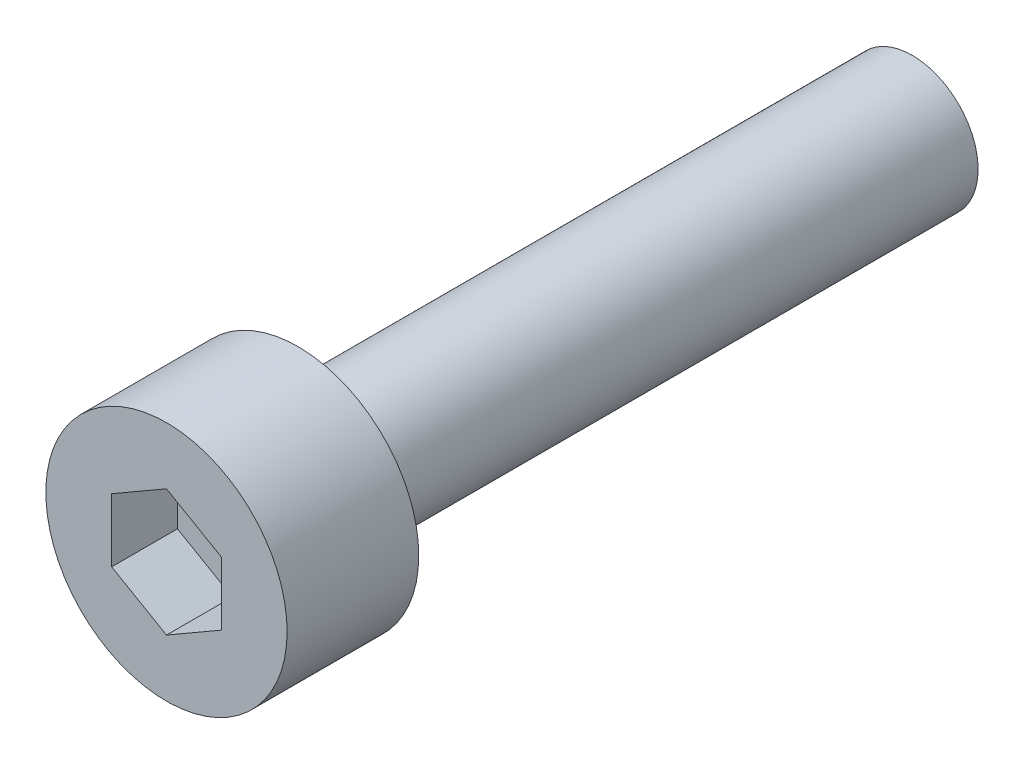
SolidWorks part; units mm, degrees
material "灰铸铁"
ref_plane "前视基准面" through (0, 0, 0) normal (0, 0, 1) x (1, 0, 0)
ref_plane "上视基准面" through (0, 0, 0) normal (0, 1, 0) x (1, 0, 0)
ref_plane "右视基准面" through (0, 0, 0) normal (1, 0, 0) x (0, 0, -1)
sketch "草图1" plane through (0, 0, 0) normal (0, 0, 1) x (1, 0, 0)
  circle A0 centre (0, 0) radius 2.75
  dimension "D1" = 5.5
extrude "凸台-拉伸1" add sketch "草图1" along normal blind 3
sketch "草图2" plane through (0, 0, 3) normal (0, 0, 1) x (1, 0, 0)
  line L1 (0, -1.4434) -> (1.25, -0.7217)
  line L2 (1.25, -0.7217) -> (1.25, 0.7217)
  line L3 (1.25, 0.7217) -> (0, 1.4434)
  line L4 (0, 1.4434) -> (-1.25, 0.7217)
  line L5 (-1.25, 0.7217) -> (-1.25, -0.7217)
  line L6 (-1.25, -0.7217) -> (0, -1.4434)
  circle A0 centre (0, 0) radius 1.25 construction
  dimension "D1" = 2.5
extrude "切除-拉伸1" cut sketch "草图2" against normal blind 1.5
sketch "草图3" plane through (0, 0, 0) normal (0, 0, -1) x (-1, 0, 0)
  circle A0 centre (0, 0) radius 1.5
extrude "凸台-拉伸2" add sketch "草图3" along normal blind 14
